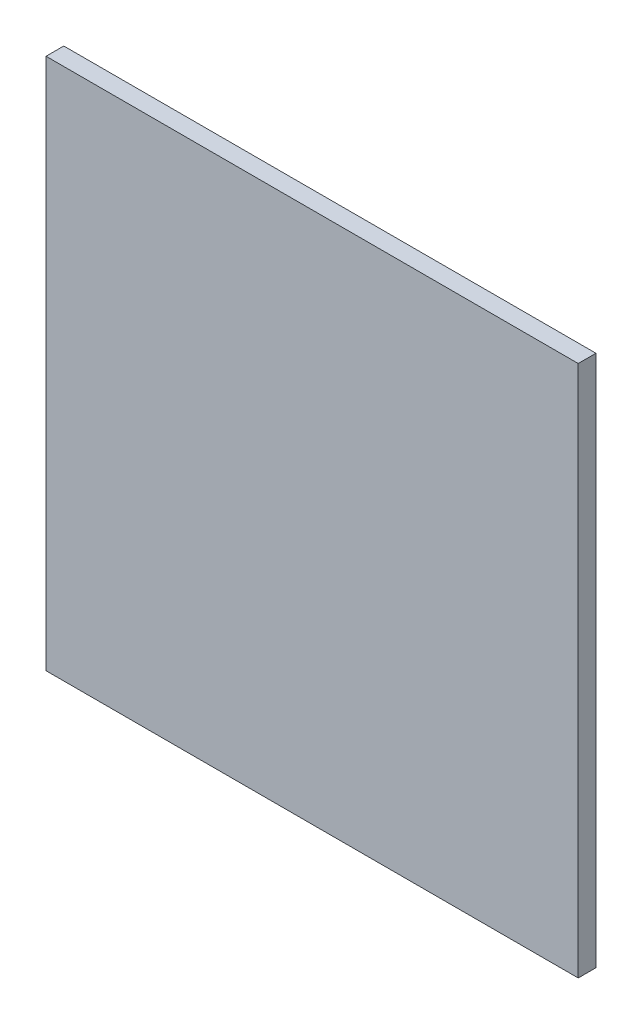
SolidWorks part; units mm, degrees
ref_plane "Plan de face" through (0, 0, 0) normal (0, 0, 1) x (1, 0, 0)
ref_plane "Plan de dessus" through (0, 0, 0) normal (0, 1, 0) x (1, 0, 0)
ref_plane "Plan de droite" through (0, 0, 0) normal (1, 0, 0) x (0, 0, -1)
sketch "Esquisse1" plane through (0, 0, 0) normal (0, 0, 1) x (1, 0, 0)
  line L1 (0, 0) -> (300, 0)
  line L2 (0, 0) -> (0, 300)
  line L3 (0, 300) -> (300, 300)
  line L4 (300, 0) -> (300, 300)
  dimension "D1" = 300
  dimension "D2" = 300
extrude "Boss.-Extru.1" add sketch "Esquisse1" along normal blind 10
